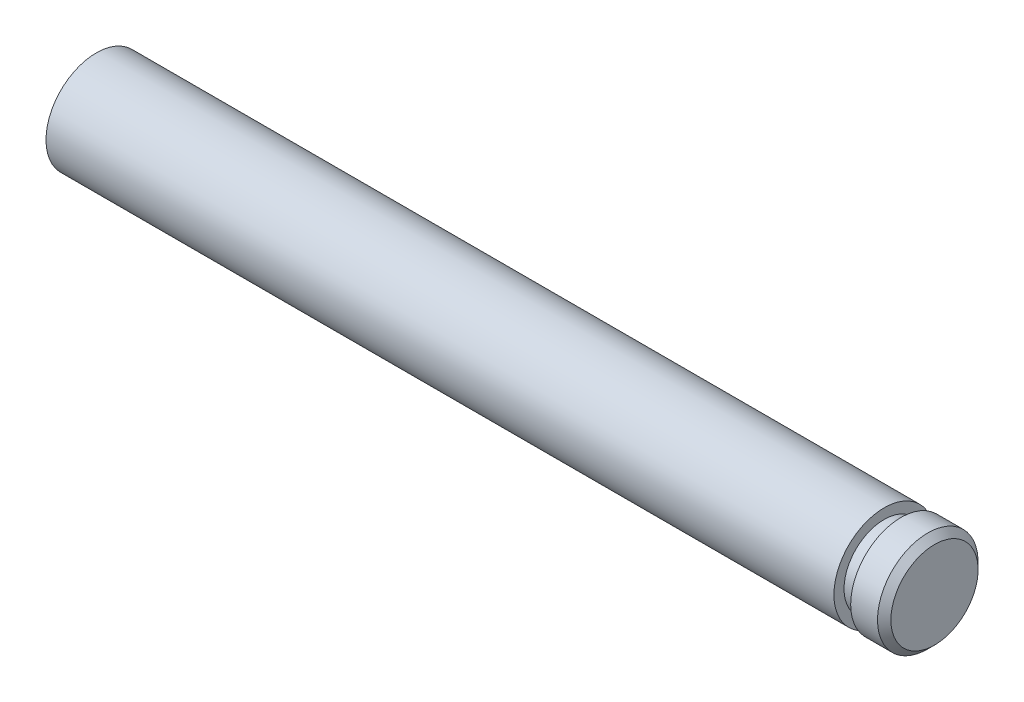
SolidWorks part; units mm, degrees
material "201 Acero inoxidable recocido (SS)"
ref_plane "Alzado" through (0, 0, 0) normal (0, 0, 1) x (1, 0, 0)
ref_plane "Planta" through (0, 0, 0) normal (0, 1, 0) x (1, 0, 0)
ref_plane "Vista lateral" through (0, 0, 0) normal (1, 0, 0) x (0, 0, -1)
sketch "Croquis1" plane through (0, 0, 0) normal (0, 1, 0) x (1, 0, 0)
  line L0 (0, 0) -> (25, 0)
  line L1 (25, 0) -> (25, 1.5)
  line L2 (25, 1.5) -> (24, 1.5)
  line L3 (24, 1.5) -> (24, 1.1983)
  line L4 (24, 1.1983) -> (23.5, 1.1983)
  line L5 (23.5, 1.1983) -> (23.5, 1.5)
  line L6 (23.5, 1.5) -> (0, 1.5)
  line L7 (0, 1.5) -> (0, 0)
  dimension "D1" = 1.5
  dimension "D2" = 25
  dimension "D3" = 1
  dimension "D4" = 0.5
revolve "Revolución1" add sketch "Croquis1" angle 360 about L0
chamfer "Chaflán1" distance 0.2 angle 45 1 edges at (25, 0, 1.5)
